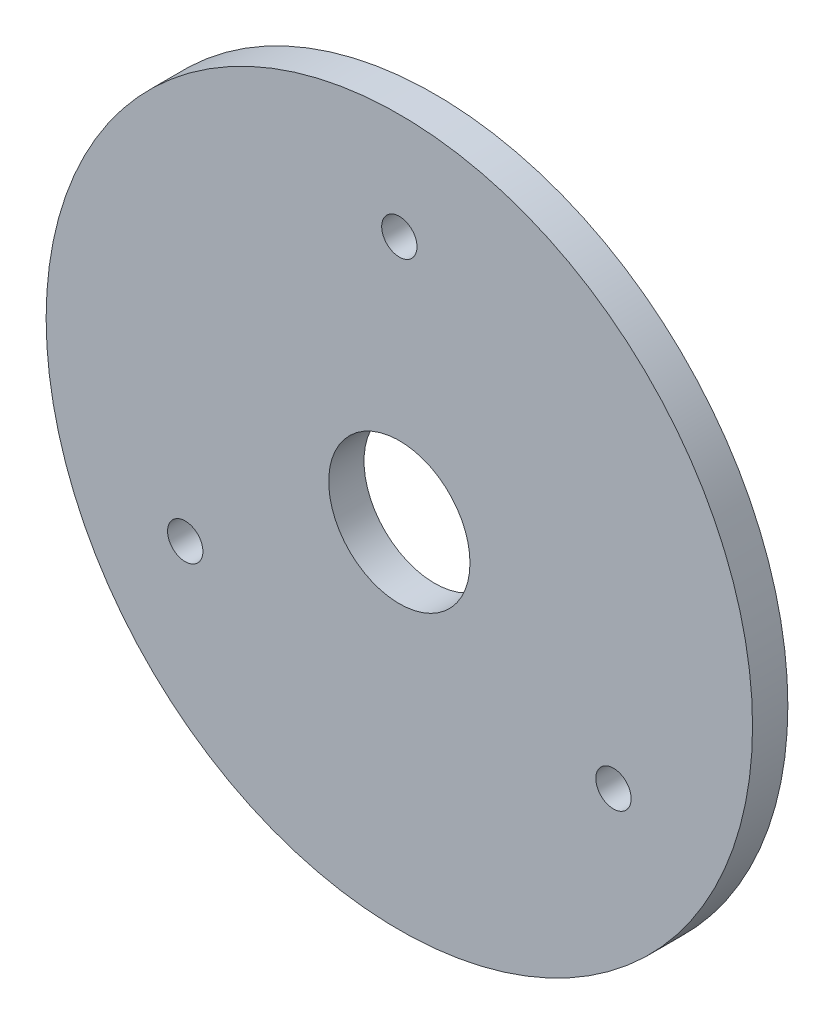
SolidWorks part; units mm, degrees
ref_plane "前视基准面" through (0, 0, 0) normal (0, 0, 1) x (1, 0, 0)
ref_plane "上视基准面" through (0, 0, 0) normal (0, 1, 0) x (1, 0, 0)
ref_plane "右视基准面" through (0, 0, 0) normal (1, 0, 0) x (0, 0, -1)
sketch "草图1" plane through (0, 0, 0) normal (0, 0, 1) x (1, 0, 0)
  circle A0 centre (0, 0) radius 20
  dimension "D1" = 40
extrude "凸台-拉伸1" add sketch "草图1" along normal blind 2
sketch "草图2" plane through (0, 0, 2) normal (0, 0, 1) x (1, 0, 0)
  circle A0 centre (0, 14) radius 1
  dimension "D1" = 2
  dimension "D2" = 14
extrude "切除-拉伸1" cut sketch "草图2" against normal blind 2
pattern_circular "阵列(圆周)1" count 3 over 360 about axis through (0, 0, 0) along (0, 0, 1) of "切除-拉伸1"
sketch "草图3" plane through (0, 0, 2) normal (0, 0, 1) x (1, 0, 0)
  circle A0 centre (0, 0) radius 4
  dimension "D1" = 8
extrude "切除-拉伸2" cut sketch "草图3" against normal blind 2
